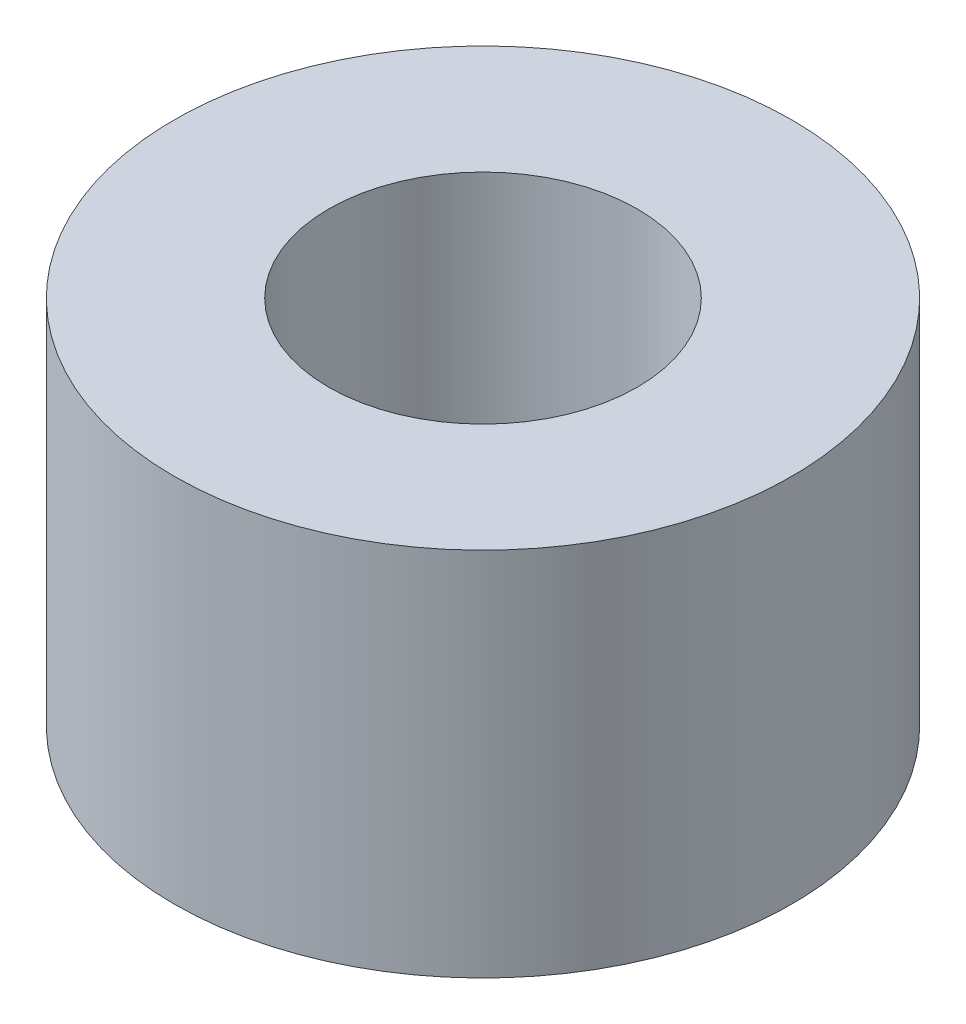
SolidWorks part; units mm, degrees
ref_plane "Front Plane" through (0, 0, 0) normal (0, 0, 1) x (1, 0, 0)
ref_plane "Top Plane" through (0, 0, 0) normal (0, 1, 0) x (1, 0, 0)
ref_plane "Right Plane" through (0, 0, 0) normal (1, 0, 0) x (0, 0, -1)
sketch "Sketch2" plane through (0, 0, 0) normal (0, 1, 0) x (1, 0, 0)
  circle A0 centre (0, 0) radius 2.5
  circle A1 centre (0, 0) radius 1.25
  dimension "D1" = 5
  dimension "D2" = 2.5
extrude "Boss-Extrude1" add sketch "Sketch2" along normal blind 3
